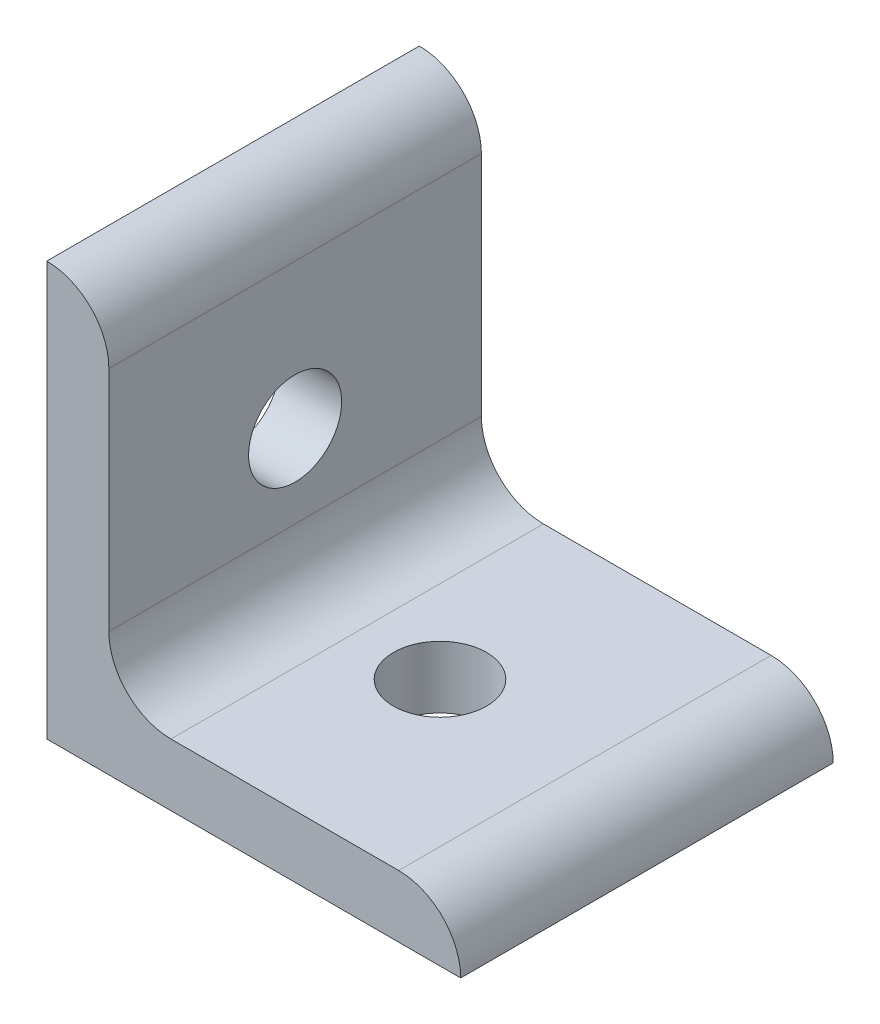
SolidWorks part; units mm, degrees
ref_plane "Front Plane" through (0, 0, 0) normal (0, 0, 1) x (1, 0, 0)
ref_plane "Top Plane" through (0, 0, 0) normal (0, 1, 0) x (1, 0, 0)
ref_plane "Right Plane" through (0, 0, 0) normal (1, 0, 0) x (0, 0, -1)
sketch "Sketch1" plane through (0, 0, 0) normal (0, 0, 1) x (1, 0, 0)
  line L0 (0, 0) -> (0, 40)
  line L1 (6, 34) -> (6, 40) construction
  line L2 (6, 34) -> (6, 12)
  line L3 (12, 6) -> (34, 6)
  line L4 (6, 40) -> (0, 40) construction
  line L5 (40, 0) -> (0, 0)
  line L6 (34, 6) -> (40, 6) construction
  line L7 (40, 6) -> (40, 0) construction
  arc A0 (6, 34) -> (0, 40) centre (0, 34) ccw
  arc A1 (40, 0) -> (34, 6) centre (34, 0) ccw
  arc A2 (6, 12) -> (12, 6) centre (12, 12) ccw
  point P10 (6, 37)
  dimension "E" = 6
  dimension "D" = 6
  dimension "C" = 40
  dimension "B" = 40
extrude "Boss-Extrude1" add sketch "Sketch1" along normal mid plane 36
sketch "Sketch2" plane through (0, 0, 0) normal (0, 1, 0) x (1, 0, 0)
  line L0 (0, 0) -> (20, 0) construction
  circle A0 centre (20, 0) radius 4.5
extrude "Cut-Extrude1" cut sketch "Sketch2" along normal through all
sketch "Sketch3" plane through (0, 0, 0) normal (1, 0, 0) x (0, 0, -1)
  line L0 (0, 0) -> (0, 20) construction
  circle A0 centre (0, 20) radius 4.5
  dimension "D1" = 20
extrude "Cut-Extrude2" cut sketch "Sketch3" along normal through all
equation "\"E@Sketch3\" = \"E@Sketch2\""
equation "\"D1@Sketch3\" = \"D1@Sketch2\""
